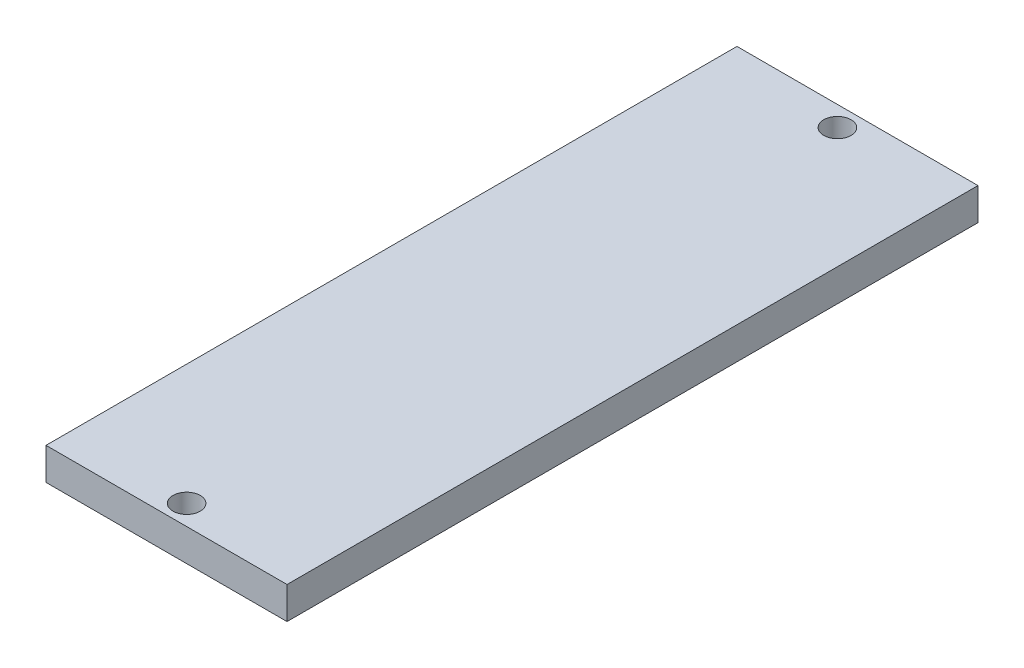
SolidWorks part; units mm, degrees
ref_plane "前视基准面" through (0, 0, 0) normal (0, 0, 1) x (1, 0, 0)
ref_plane "上视基准面" through (0, 0, 0) normal (0, 1, 0) x (1, 0, 0)
ref_plane "右视基准面" through (0, 0, 0) normal (1, 0, 0) x (0, 0, -1)
sketch "草图1" plane through (0, 0, 0) normal (0, 1, 0) x (1, 0, 0)
  line L1 (-15, 43) -> (15, 43)
  line L2 (-15, 43) -> (-15, -43)
  line L3 (-15, -43) -> (15, -43)
  line L4 (15, 43) -> (15, -43)
  line L5 (-15, 43) -> (15, -43) construction
  line L6 (-15, -43) -> (15, 43) construction
  circle A0 centre (0, 40.5) radius 1.7
  circle A1 centre (0, -40.5) radius 1.7
  point P0 (0, 0)
  dimension "D3" = 3.4
  dimension "D4" = 2.5
  dimension "D5" = 3.4
  dimension "D6" = 2.5
  dimension "D1" = 86
  dimension "D2" = 30
extrude "凸台-拉伸1" add sketch "草图1" along normal blind 4
